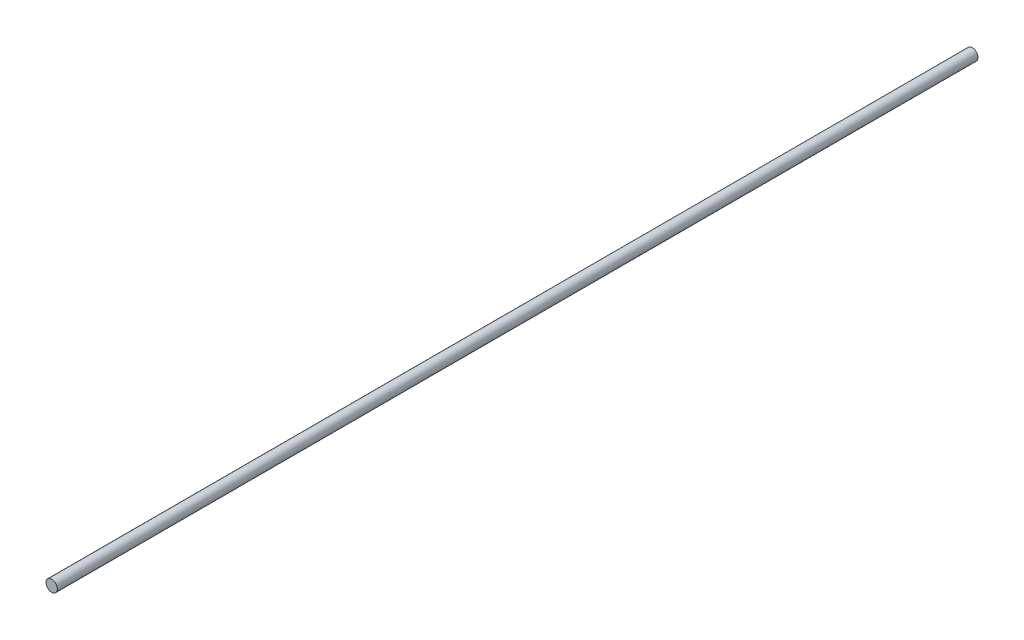
SolidWorks part; units mm, degrees
ref_plane "Plan de face" through (0, 0, 0) normal (0, 0, 1) x (1, 0, 0)
ref_plane "Plan de dessus" through (0, 0, 0) normal (0, 1, 0) x (1, 0, 0)
ref_plane "Plan de droite" through (0, 0, 0) normal (1, 0, 0) x (0, 0, -1)
sketch "Esquisse1" plane through (0, 0, 0) normal (0, 0, 1) x (1, 0, 0)
  circle A0 centre (0, 0) radius 4
  dimension "D1" = 8
extrude "Boss.-Extru.1" add sketch "Esquisse1" along normal blind 648
